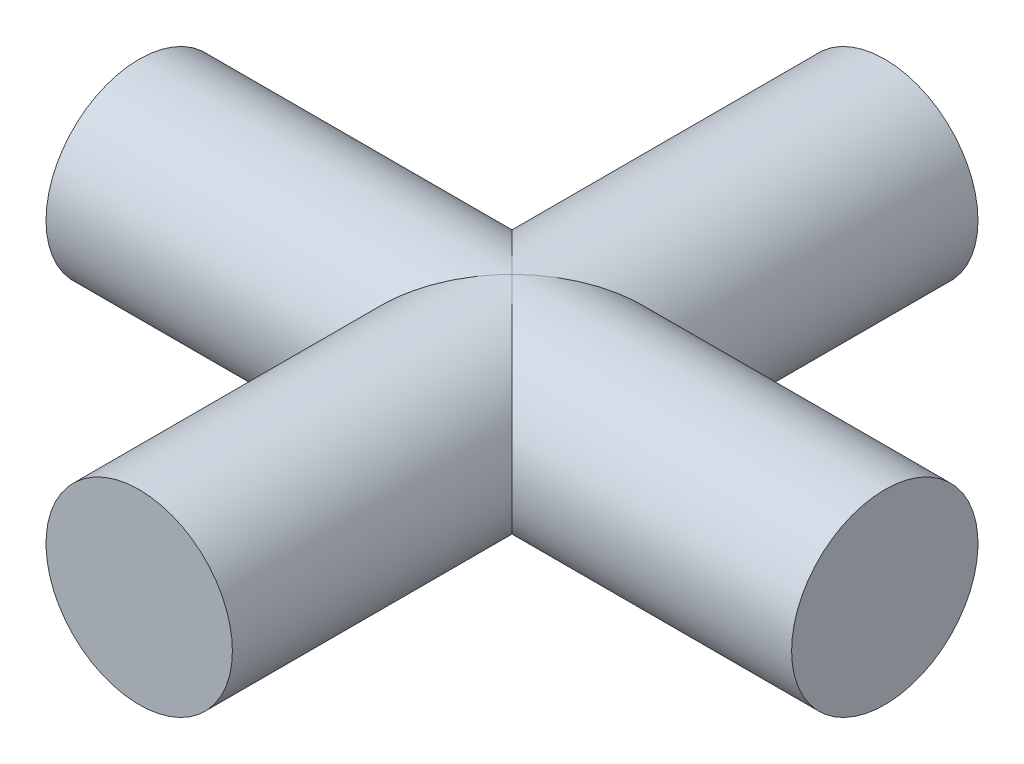
SolidWorks part; units mm, degrees
ref_plane "Front Plane" through (0, 0, 0) normal (0, 0, 1) x (1, 0, 0)
ref_plane "Top Plane" through (0, 0, 0) normal (0, 1, 0) x (1, 0, 0)
ref_plane "Right Plane" through (0, 0, 0) normal (1, 0, 0) x (0, 0, -1)
sketch "Sketch1" plane through (0, 0, 0) normal (0, 0, 1) x (1, 0, 0)
  circle A0 centre (0, 0) radius 6.35
  dimension "D1" = 12.7
extrude "Boss-Extrude1" add sketch "Sketch1" along normal blind 50.8
ref_plane "Plane1" through (0, 0, 25.4) normal (0, 0, 1) x (1, 0, 0)
sketch "Sketch2" plane through (0, 0, 25.4) normal (0, 0, 1) x (1, 0, 0)
  line L0 (0, 6.35) -> (0, -6.35) construction
pattern_circular "CirPattern1" count 2 over 90 about axis through (0, 6.35, 25.4) along (0, -1, 0) of "Boss-Extrude1"
